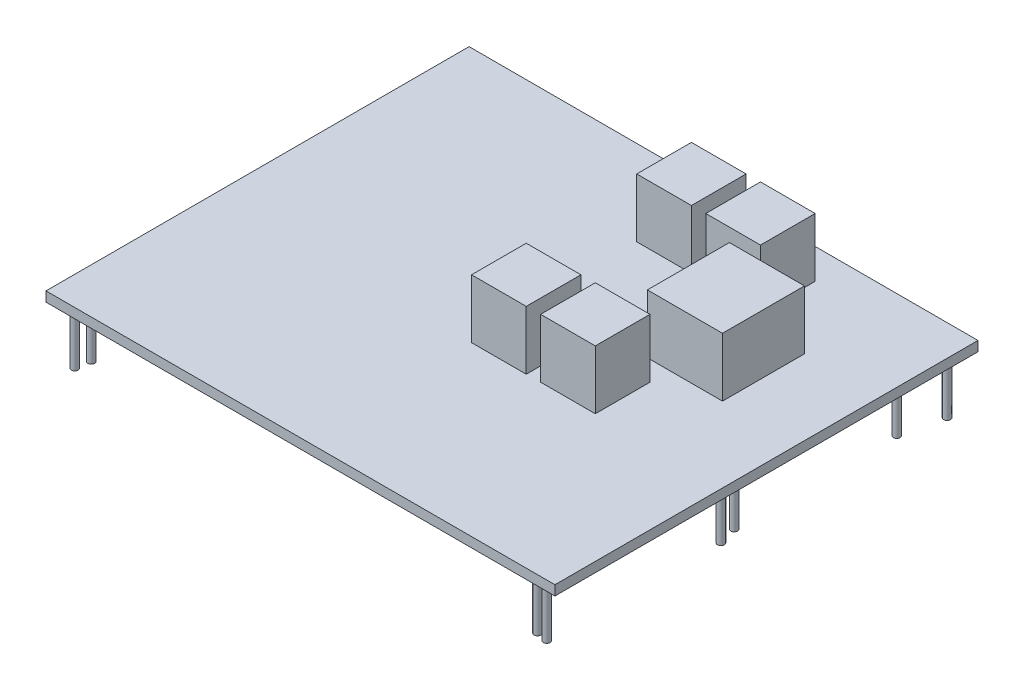
SolidWorks part; units mm, degrees
ref_plane "Front Plane" through (0, 0, 0) normal (0, 0, 1) x (1, 0, 0)
ref_plane "Top Plane" through (0, 0, 0) normal (0, 1, 0) x (1, 0, 0)
ref_plane "Right Plane" through (0, 0, 0) normal (1, 0, 0) x (0, 0, -1)
sketch "Sketch2" plane through (0, 0, 0) normal (0, 1, 0) x (1, 0, 0)
  line L1 (-326.5722, 108.1905) -> (-66.8622, 108.1905)
  line L2 (-326.5722, 108.1905) -> (-326.5722, -107.7095)
  line L3 (-326.5722, -107.7095) -> (-66.8622, -107.7095)
  line L4 (-66.8622, 108.1905) -> (-66.8622, -107.7095)
extrude "Boss-Extrude1" add sketch "Sketch2" along normal blind 5
sketch "Sketch1" plane through (0, 0, 0) normal (0, 1, 0) x (1, 0, 0)
  line L0 (-326.5722, 108.1905) -> (-66.8622, 108.1905) construction
  line L1 (-326.5722, 108.1905) -> (-326.5722, -107.7095) construction
  line L2 (-326.5722, -107.7095) -> (-66.8622, -107.7095) construction
  line L3 (-66.8622, 108.1905) -> (-66.8622, -107.7095) construction
  line L4 (-326.5722, 108.1905) -> (-66.8622, -107.7095) construction
  line L5 (-326.5722, -107.7095) -> (-66.8622, 108.1905) construction
  circle A0 centre (-320.0922, 101.1705) radius 1.75
  circle A1 centre (-312.8522, 99.8505) radius 1.75
  circle A2 centre (-318.8322, -92.3095) radius 1.75
  circle A3 centre (-320.1022, -99.4895) radius 1.75
  circle A4 centre (-177.8622, -34.3995) radius 1.75
  circle A5 centre (-170.2422, -34.3995) radius 1.75
  circle A6 centre (-104.3822, -25.1495) radius 1.75
  circle A7 centre (-216.1422, -6.7695) radius 1.75
  circle A8 centre (-77.9922, -11.8595) radius 1.75
  circle A9 centre (-80.7022, -2.3895) radius 1.75
  circle A10 centre (-84.9022, -98.5295) radius 1.75
  circle A11 centre (-79.2598, -99.4895) radius 1.75
  circle A12 centre (-104.3722, 71.8805) radius 1.75
  circle A13 centre (-80.5422, 80.4105) radius 1.75
  circle A14 centre (-75.6222, 101.1705) radius 1.75
  circle A15 centre (-224.8422, 89.7805) radius 1.75
  point P1 (-196.7172, 0.2405)
  dimension "D3" = 3.5
  dimension "D1" = 215.9
  dimension "D2" = 259.71
  dimension "D4" = 6.48
  dimension "D5" = 7.24
  dimension "D6" = 111
  dimension "D7" = 103.38
  dimension "D8" = 18.04
  dimension "D9" = 12.3976
  dimension "D10" = 37.52
  dimension "D11" = 11.13
  dimension "D12" = 13.84
  dimension "D13" = 110.43
  dimension "D14" = 101.73
  dimension "D15" = 7.74
  dimension "D16" = 6.47
  dimension "D17" = 37.51
  dimension "D18" = 13.68
  dimension "D19" = 8.76
  dimension "D20" = 15.4
  dimension "D21" = 8.22
  dimension "D22" = 100.94
  dimension "D23" = 7.02
  dimension "D24" = 8.34
  dimension "D25" = 18.41
  dimension "D26" = 36.31
  dimension "D27" = 27.78
  dimension "D28" = 7.02
  dimension "D29" = 8.22
  dimension "D30" = 9.18
  dimension "D31" = 73.31
  dimension "D32" = 73.31
  dimension "D33" = 82.56
  dimension "D34" = 105.32
  dimension "D35" = 95.85
extrude "Boss-Extrude2" add sketch "Sketch1" against normal blind 30
sketch "fans" plane through (0, 5, 0) normal (0, 1, 0) x (1, 0, 0)
  line L0 (-160.0056, 6.041) -> (-132.1047, 6.041)
  line L1 (-143.5588, 58.0246) -> (-105.2318, 58.0246)
  line L2 (-143.5588, 58.0246) -> (-143.5588, 16.1734)
  line L3 (-143.5588, 16.1734) -> (-105.2318, 16.1734)
  line L4 (-105.2318, 58.0246) -> (-105.2318, 16.1734)
  line L5 (-195.1019, 5.8941) -> (-167.201, 5.8941)
  line L6 (-195.1019, 5.8941) -> (-195.1019, -22.0067)
  line L7 (-195.1019, -22.0067) -> (-167.201, -22.0067)
  line L8 (-167.201, 5.8941) -> (-167.201, -22.0067)
  line L9 (-160.0056, 6.041) -> (-160.0056, -21.8599)
  line L10 (-160.0056, -21.8599) -> (-132.1047, -21.8599)
  line L11 (-132.1047, 6.041) -> (-132.1047, -21.8599)
  line L12 (-162.4285, 92.7538) -> (-134.5277, 92.7538)
  line L13 (-197.5248, 92.607) -> (-169.624, 92.607)
  line L14 (-197.5248, 92.607) -> (-197.5248, 64.7061)
  line L15 (-197.5248, 64.7061) -> (-169.624, 64.7061)
  line L16 (-169.624, 92.607) -> (-169.624, 64.7061)
  line L17 (-162.4285, 92.7538) -> (-162.4285, 64.853)
  line L18 (-162.4285, 64.853) -> (-134.5277, 64.853)
  line L19 (-134.5277, 92.7538) -> (-134.5277, 64.853)
extrude "Boss-Extrude3" add sketch "fans" along normal blind 30
